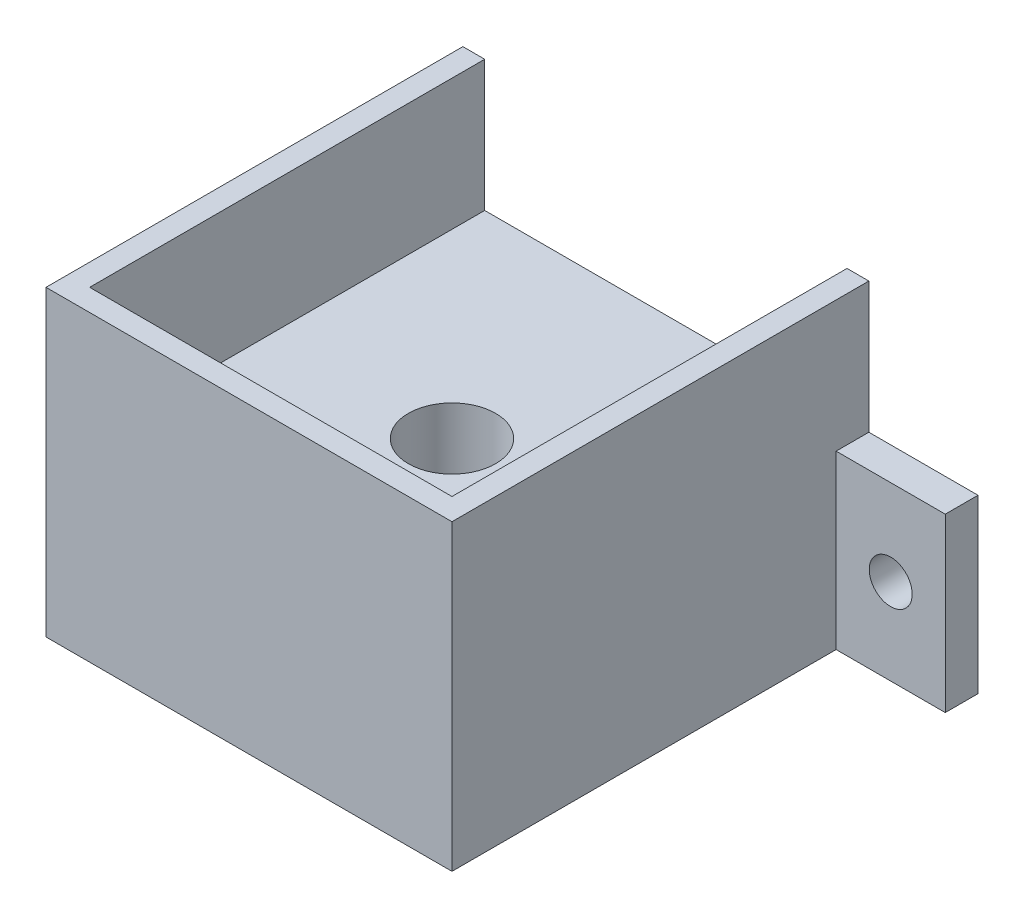
SolidWorks part; units mm, degrees
ref_plane "Front Plane" through (0, 0, 0) normal (0, 0, 1) x (1, 0, 0)
ref_plane "Top Plane" through (0, 0, 0) normal (0, 1, 0) x (1, 0, 0)
ref_plane "Right Plane" through (0, 0, 0) normal (1, 0, 0) x (0, 0, -1)
sketch "Sketch1" plane through (0, 0, 0) normal (0, 1, 0) x (1, 0, 0)
  line L1 (-23.622, -24.257) -> (23.622, -24.257)
  line L2 (-23.622, -24.257) -> (-23.622, 20.447)
  line L3 (-23.622, 24.257) -> (23.622, 24.257)
  line L4 (23.622, -24.257) -> (23.622, 20.447)
  line L5 (-23.622, -24.257) -> (23.622, 24.257) construction
  line L6 (-23.622, 24.257) -> (23.622, -24.257) construction
  line L7 (23.622, 24.257) -> (36.322, 24.257)
  line L9 (23.622, 20.447) -> (36.322, 20.447)
  line L10 (36.322, 24.257) -> (36.322, 20.447)
  line L11 (-23.622, 24.257) -> (-36.322, 24.257)
  line L13 (-23.622, 20.447) -> (-36.322, 20.447)
  line L14 (-36.322, 24.257) -> (-36.322, 20.447)
  point P0 (0, 0)
  point P12 (23.622, -24.257)
  point P13 (-36.322, 20.447)
  point P14 (-23.622, 20.447)
  point P15 (-23.622, -24.257)
  point P16 (-23.622, 24.257)
  point P17 (23.622, 20.447)
  point P18 (36.322, 20.447)
  point P19 (36.322, 24.257)
  point P20 (23.622, 24.257)
  point P21 (-23.622, 24.257)
  point P22 (-23.6917, 24.1855)
  point P23 (-23.6917, 20.3755)
  point P24 (23.5523, 20.3755)
  point P25 (-23.6917, 24.1855)
  point P26 (-23.6917, 20.3755)
  point P27 (-36.3917, 20.3755)
  point P28 (-36.3917, 24.1855)
  point P29 (23.8318, -24.3285)
  point P30 (0, 0)
  point P31 (0, 0)
  point P32 (23.4813, 20.5899)
  point P33 (0, 0)
  dimension "D1" = 47.244
  dimension "D2" = 48.514
  dimension "D3" = 3.81
  dimension "D5" = 12.7
  dimension "D6" = 12.7
extrude "Boss-Extrude1" add sketch "Sketch1" along normal blind 20
sketch "Sketch2" plane through (0, 20, 0) normal (0, 1, 0) x (1, 0, 0)
  line L0 (36.322, 24.257) -> (-36.322, 24.257) construction
  line L1 (-23.622, 24.257) -> (-21.082, 24.257)
  line L2 (-23.622, 24.257) -> (-23.622, -24.257)
  line L3 (-23.622, -24.257) -> (-21.6685, -24.257)
  line L4 (-21.082, 24.257) -> (-21.082, -21.717)
  line L5 (-23.622, -24.257) -> (23.622, -24.257) construction
  line L6 (23.622, -24.257) -> (23.622, 20.447) construction
  line L7 (-21.6685, -24.257) -> (23.622, -24.257)
  line L9 (-21.082, -21.717) -> (21.082, -21.717)
  line L10 (23.622, -24.257) -> (23.622, -21.8919)
  line L11 (-23.622, 20.447) -> (-23.622, -24.257) construction
  line L12 (21.5196, -24.257) -> (23.622, -24.257)
  line L13 (21.082, -21.717) -> (21.082, 24.257)
  line L14 (21.082, 24.257) -> (23.622, 24.257)
  line L15 (23.622, -24.257) -> (23.622, 24.257)
  dimension "D1" = 2.54
  dimension "D2" = 2.54
  dimension "D3" = 2.54
extrude "Boss-Extrude2" add sketch "Sketch2" along normal blind 15.24 contours L7 L3 L2 L1 L4 L9 L13 L14 L15
sketch "Sketch3" plane through (0, 0, -20.447) normal (0, 0, 1) x (1, 0, 0)
  line L0 (23.622, 10) -> (36.322, 10) construction
  line L1 (23.622, 20) -> (23.622, 0) construction
  line L2 (36.322, 20) -> (36.322, 0) construction
  line L3 (29.972, 20) -> (29.972, 0) construction
  line L4 (23.622, 20) -> (36.322, 20) construction
  line L5 (23.622, 0) -> (36.322, 0) construction
  circle A0 centre (29.972, 10) radius 2.5
  point P14 (36.322, 10)
  point P15 (0, 0)
  dimension "D1" = 5
extrude "Cut-Extrude1" cut sketch "Sketch3" against normal through all
mirror "Mirror1" about plane through (0, 0, 0) normal (1, 0, 0) of "Cut-Extrude1"
sketch "Sketch4" plane through (0, 20, 0) normal (0, 1, 0) x (1, 0, 0)
  line L0 (0, 24.257) -> (0, -21.717) construction
  line L1 (21.082, 24.257) -> (-21.082, 24.257) construction
  line L2 (-21.082, -21.717) -> (21.082, -21.717) construction
  line L3 (-21.082, -21.717) -> (21.082, -21.717) construction
  circle A0 centre (0, -0.635) radius 5.08
  dimension "D2" = 10.16
  dimension "D1" = 21.082
extrude "Cut-Extrude2" cut sketch "Sketch4" against normal through all
